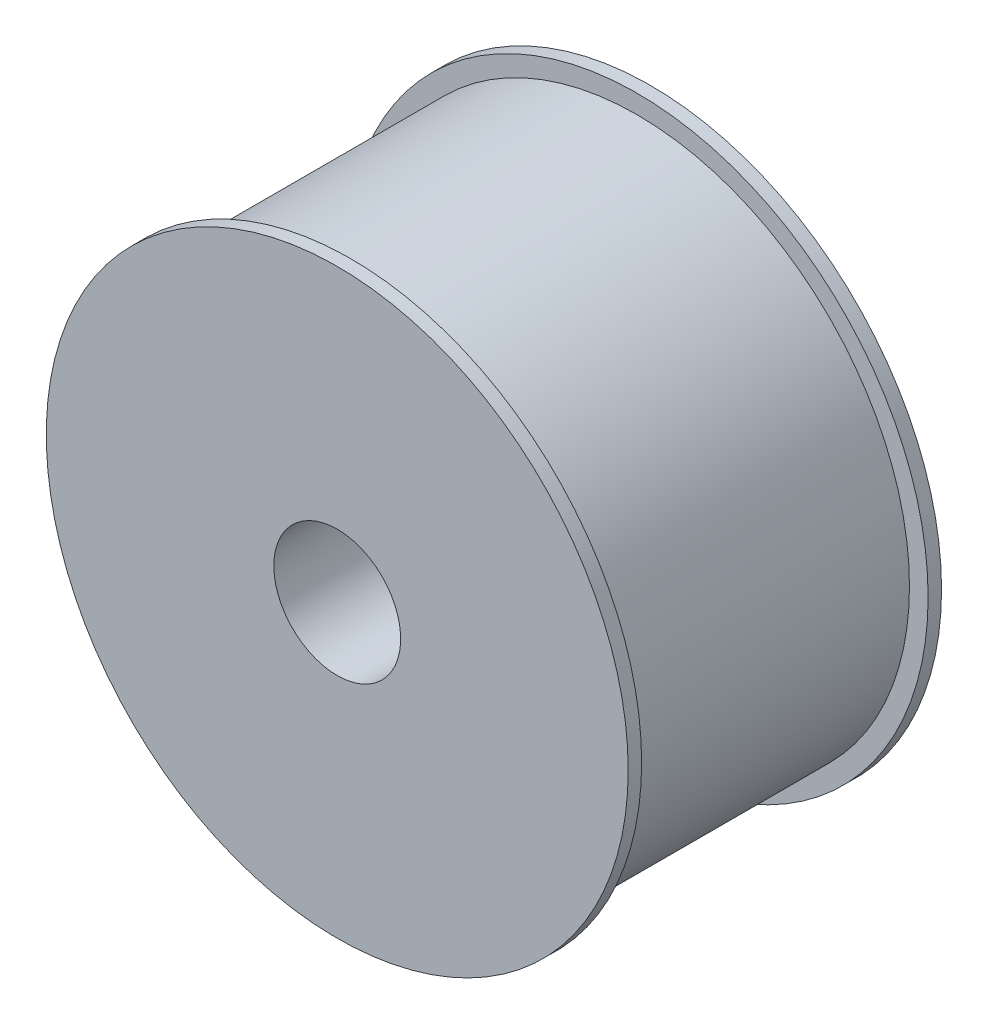
SolidWorks part; units mm, degrees
ref_plane "Alzado" through (0, 0, 0) normal (0, 0, 1) x (1, 0, 0)
ref_plane "Planta" through (0, 0, 0) normal (0, 1, 0) x (1, 0, 0)
ref_plane "Vista lateral" through (0, 0, 0) normal (1, 0, 0) x (0, 0, -1)
sketch "Croquis1" plane through (0, 0, 0) normal (0, 0, 1) x (1, 0, 0)
  circle A0 centre (0, 0) radius 36.5
extrude "Saliente-Extruir1" add sketch "Croquis1" along normal blind 38.4
sketch "Croquis2" plane through (0, 0, 38.4) normal (0, 0, 1) x (1, 0, 0)
  circle A0 centre (0, 0) radius 39
extrude "Saliente-Extruir2" add sketch "Croquis2" along normal blind 1.8
ref_plane "Plano2" through (0, 0, 19.2) normal (0, 0, -1) x (-1, 0, 0)
mirror "Simetría1" about plane through (0, 0, 19.2) normal (0, 0, -1) of "Saliente-Extruir2"
sketch "Croquis3" plane through (0, 0, -1.8) normal (0, 0, -1) x (-1, 0, 0)
  circle A0 centre (0, 0) radius 8.5
extrude "Cortar-Extruir1" cut sketch "Croquis3" against normal through all
